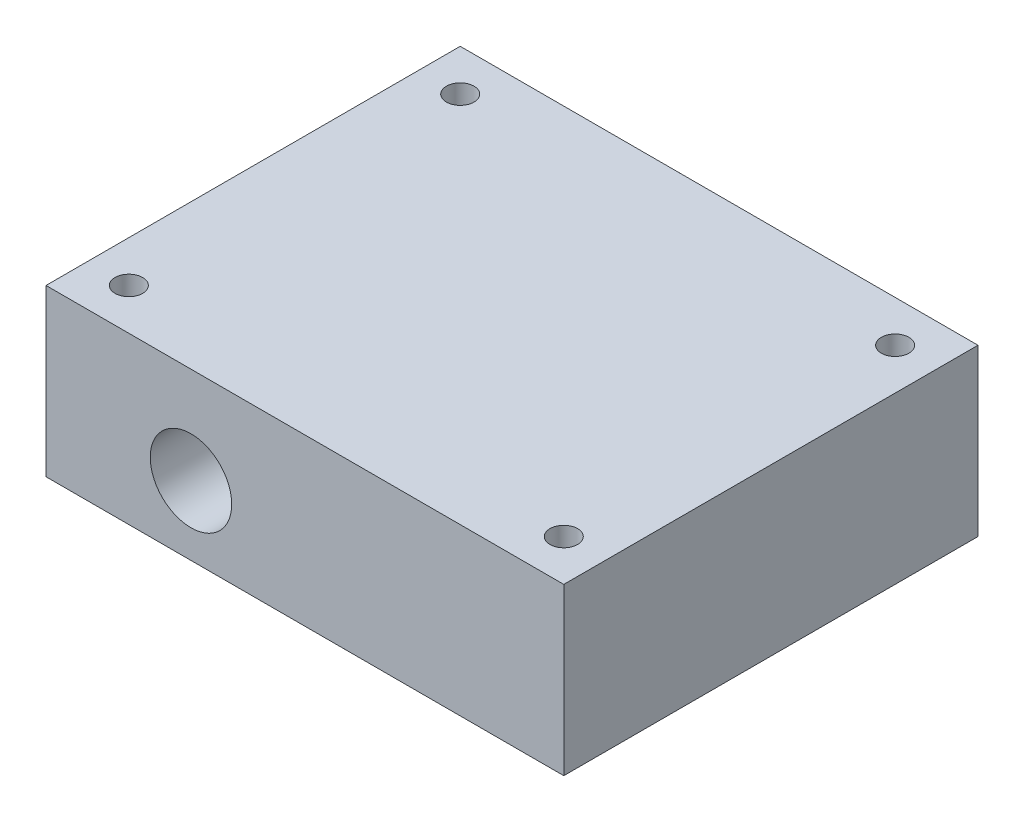
SolidWorks part; units mm, degrees
ref_plane "Front" through (0, 0, 0) normal (0, 0, 1) x (1, 0, 0)
ref_plane "Top" through (0, 0, 0) normal (0, 1, 0) x (1, 0, 0)
ref_plane "Right" through (0, 0, 0) normal (1, 0, 0) x (0, 0, -1)
sketch "Sketch1" plane through (0, 0, 0) normal (0, 1, 0) x (1, 0, 0)
  line L1 (0, 0) -> (75, 0)
  line L2 (0, 0) -> (0, 60)
  line L3 (0, 60) -> (75, 60)
  line L4 (75, 0) -> (75, 60)
  dimension "D1" = 60
  dimension "D2" = 75
extrude "Boss-Extrude1" add sketch "Sketch1" along normal blind 24
sketch "Sketch2" plane through (0, 24, 0) normal (0, 1, 0) x (1, 0, 0)
  line L0 (0, 60) -> (0, 0) construction
  line L1 (75, 60) -> (0, 60) construction
  line L2 (0, 30) -> (75, 30) construction
  line L3 (75, 0) -> (75, 60) construction
  line L5 (37.5, 60) -> (37.5, 0) construction
  line L6 (0, 0) -> (75, 0) construction
  circle A0 centre (6, 54) radius 2
  circle A1 centre (6, 6) radius 2
  circle A2 centre (69, 54) radius 2
  circle A3 centre (69, 6) radius 2
  dimension "D1" = 4
  dimension "D2" = 6
  dimension "D3" = 6
extrude "Cut-Extrude1" cut sketch "Sketch2" against normal through all
sketch "Sketch3" plane through (0, 0, 0) normal (0, -1, 0) x (1, 0, 0)
  line L0 (0, 0) -> (75, 0) construction
  line L1 (15, -10) -> (60, -10)
  line L2 (15, -10) -> (15, -50)
  line L3 (15, -50) -> (60, -50)
  line L4 (60, -10) -> (60, -50)
  line L5 (0, -60) -> (0, 0) construction
  line L6 (75, 0) -> (75, -60) construction
  line L7 (0, -30) -> (75, -30) construction
  dimension "D1" = 10
  dimension "D2" = 15
  dimension "D3" = 15
extrude "Cut-Extrude2" cut sketch "Sketch3" against normal blind 15
sketch "Sketch4" plane through (0, 0, -10) normal (0, 0, -1) x (-1, 0, 0)
  line L0 (-15, 15) -> (-15, 0) construction
  line L2 (-60, 0) -> (-15, 0) construction
  circle A0 centre (-21, 10) radius 5
  point P6 (-27.8637, 0)
  point P7 (0, 0)
  dimension "D1" = 10
  dimension "D2" = 6
  dimension "D3" = 10
extrude "Cut-Extrude3" cut sketch "Sketch4" against normal through all
sketch "Sketch5" plane through (0, 0, 0) normal (0, 0, 1) x (1, 0, 0)
  circle A0 centre (21, 10) radius 5.9
  dimension "D1" = 11.8
extrude "Cut-Extrude4" cut sketch "Sketch5" against normal blind 10
equation "\"d_racor\"= 11.8"
equation "\"h_alphasense\"= 5"
equation "\"h_chamber\"= 13"
equation "\"d_alphasense\" = 32.4mm"
equation "\"d_chamber\"= 19"
equation "\"h_base\"= 25 - \"h_chamber\" - \"h_alphasense\"-1"
equation "\"d_thread_sck_hole\"= 2.5"
equation "\"d_thread_sck_tap\" = 2.05"
equation "\"length_thread\"=10"
equation "\"clip_thread_hole\" = 4"
equation "\"clip_thread_tap_drill\" = 3.5"
equation "\"length_racor\"= 10"
equation "\"d_pipe\"=8"
equation "\"d_ring\"=1.8"
equation "\"D1@Sketch2\"=\"clip_thread_hole\""
equation "\"D1@Sketch5\"=\"d_racor\""
equation "\"D1@Cut-Extrude4\"=\"length_racor\""
